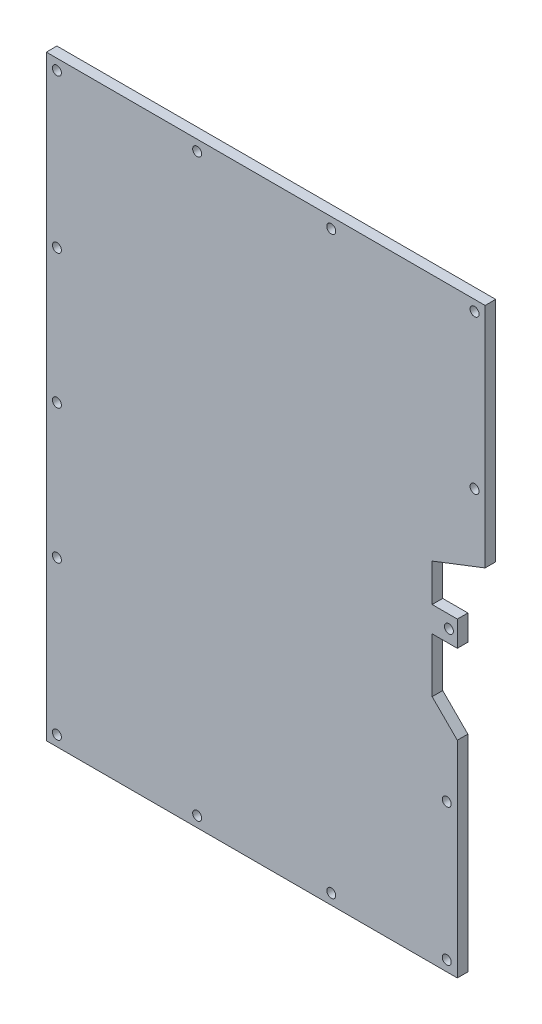
SolidWorks part; units mm, degrees
ref_plane "Front Plane" through (0, 0, 0) normal (0, 0, 1) x (1, 0, 0)
ref_plane "Top Plane" through (0, 0, 0) normal (0, 1, 0) x (1, 0, 0)
ref_plane "Right Plane" through (0, 0, 0) normal (1, 0, 0) x (0, 0, -1)
sketch "Sketch1" plane through (0, 0, 0) normal (0, 0, 1) x (1, 0, 0)
  line L0 (-123.825, 56.4375) -> (92.075, 56.4375) construction
  line L1 (-88.9, -56.4375) -> (90.4875, -56.4375) construction
  line L2 (-79.375, 82.55) -> (-79.375, -82.508) construction
  line L3 (3.675, 77.7875) -> (3.675, -82.55) construction
  line L4 (-1.5875, 81.7541) -> (-1.5875, -86.5541) construction
  line L5 (-11.1125, 79.375) -> (-11.1125, -84.7789) construction
  line L6 (-79.375, -56.4375) -> (-79.375, 56.4375)
  line L7 (-79.375, 56.4375) -> (3.675, 56.4375)
  line L8 (-79.375, -56.4375) -> (-1.5875, -56.4375)
  line L9 (11.1125, -50) -> (-92.075, -50) construction
  line L10 (-7.9375, -73.025) -> (-7.9375, 60.325) construction
  line L11 (-46.0375, -28.5183) -> (46.0375, -28.5183) construction
  line L12 (-7.9375, -50) -> (-7.9375, -28.5183) construction
  line L13 (-7.9375, -28.5183) -> (-11.1125, -23.8125) construction
  line L14 (-11.1125, -23.8125) -> (-11.1125, 12.7) construction
  line L15 (-11.1125, 12.7) -> (-3.5875, 15.875) construction
  line L16 (-6.35, 15.875) -> (-6.35, -60.325) construction
  line L17 (-12.7, 2.4) -> (6.35, 2.4) construction
  line L18 (-6.35, 2.4) -> (-1.5875, 2.4)
  line L19 (-12.7, -2.4) -> (6.35, -2.4) construction
  line L20 (-1.5875, 2.4) -> (-1.5875, -2.4)
  line L21 (-6.35, -2.4) -> (-1.5875, -2.4)
  line L22 (-6.35, -2.4) -> (-6.35, -12.7)
  line L23 (-6.35, -12.7) -> (-1.5875, -17.4625)
  line L24 (-1.5875, -17.4625) -> (-1.5875, -56.4375)
  line L25 (-6.35, 2.4) -> (-6.35, 9.525)
  line L26 (-6.35, 9.525) -> (3.675, 13.4052)
  line L27 (3.675, 13.4052) -> (3.675, 56.4375)
  line L28 (-98.425, 54.4375) -> (18.2301, 54.4375) construction
  line L29 (-77.375, 61.9125) -> (-77.375, -60.325) construction
  line L30 (-84.1375, -54.4375) -> (22.225, -54.4375) construction
  line L31 (-3.5875, -69.85) -> (-3.5875, 61.9125) construction
  line L32 (1.675, 63.5) -> (1.675, 7.9375) construction
  circle A0 centre (-3.175, 0) radius 0.85
  circle A1 centre (1.675, 54.4375) radius 0.85
  circle A2 centre (-25.4438, 54.4375) radius 0.85
  circle A3 centre (-50.8291, 54.4375) radius 0.85
  circle A4 centre (-77.375, 54.4375) radius 0.85
  circle A5 centre (-77.375, 25.3864) radius 0.85
  circle A6 centre (-77.375, 0) radius 0.85
  circle A7 centre (-77.375, -25.4084) radius 0.85
  circle A8 centre (-77.375, -54.4375) radius 0.85
  circle A9 centre (-50.8291, -54.4375) radius 0.85
  circle A10 centre (-25.4438, -54.4375) radius 0.85
  circle A11 centre (-3.5875, -54.4375) radius 0.85
  circle A12 centre (-3.5875, -28.5183) radius 0.85
  circle A13 centre (1.675, 25.3864) radius 0.85
  point P25 (-3.175, 0)
  dimension "D11" = 2.4
  dimension "D13" = 2
  dimension "D1" = 56.4375
  dimension "D2" = 56.4375
  dimension "D3" = 79.375
  dimension "D4" = 3.675
  dimension "D5" = 1.5875
  dimension "D6" = 11.1125
  dimension "D7" = 6.4375
  dimension "D8" = 6.35
  dimension "D9" = 27.9192
  dimension "D10" = 6.85
  dimension "D12" = 2.4
  dimension "D14" = 2
  dimension "D15" = 2
  dimension "D16" = 2
extrude "Extrude1" add sketch "Sketch1" along normal blind 2
